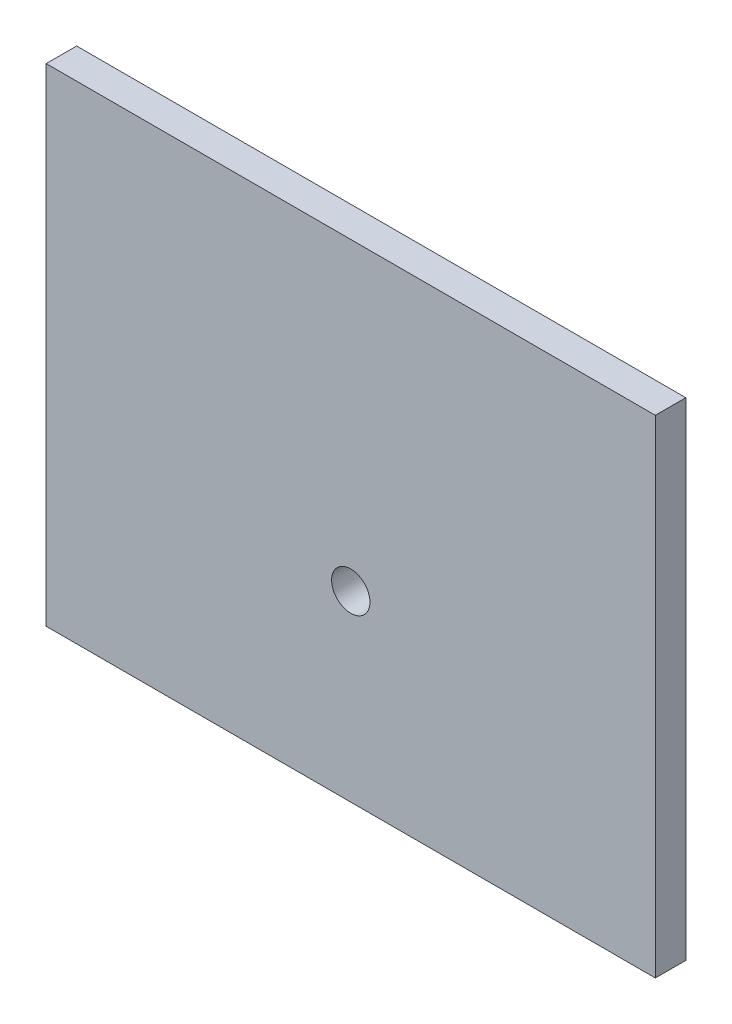
SolidWorks part; units mm, degrees
ref_plane "Front Plane" through (0, 0, 0) normal (0, 0, 1) x (1, 0, 0)
ref_plane "Top Plane" through (0, 0, 0) normal (0, 1, 0) x (1, 0, 0)
ref_plane "Right Plane" through (0, 0, 0) normal (1, 0, 0) x (0, 0, -1)
sketch "Sketch1" plane through (0, 0, 0) normal (0, 0, 1) x (1, 0, 0)
  line L0 (63.5, 38.1) -> (63.5, 101.6) construction
  line L1 (0, 0) -> (127, 0)
  line L2 (0, 0) -> (0, 101.6)
  line L3 (0, 101.6) -> (127, 101.6)
  line L4 (127, 0) -> (127, 101.6)
  line L5 (63.5, 38.1) -> (0, 38.1) construction
  circle A0 centre (63.5, 38.1) radius 4
  dimension "D3" = 8
  dimension "D1" = 127
  dimension "D2" = 101.6
extrude "Boss-Extrude1" add sketch "Sketch1" along normal blind 6.35
